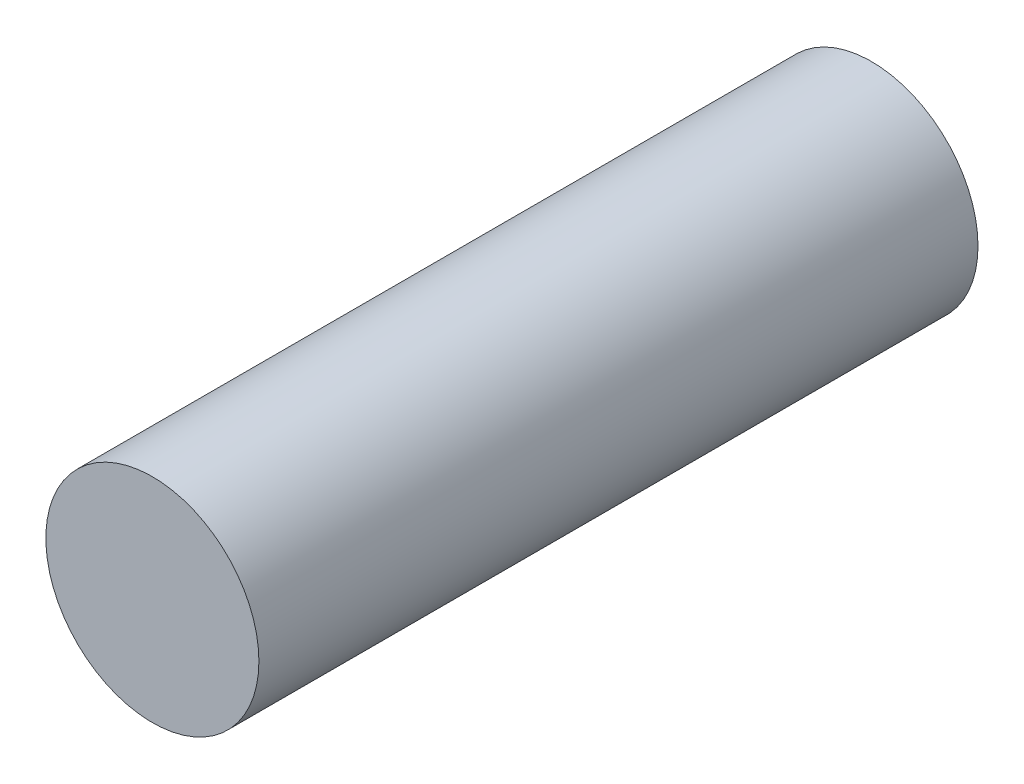
SolidWorks part; units mm, degrees
material "Cast Alloy Steel"
ref_plane "Front Plane" through (0, 0, 0) normal (0, 0, 1) x (1, 0, 0)
ref_plane "Top Plane" through (0, 0, 0) normal (0, 1, 0) x (1, 0, 0)
ref_plane "Right Plane" through (0, 0, 0) normal (1, 0, 0) x (0, 0, -1)
sketch "Sketch1" plane through (0, 0, 0) normal (0, 0, 1) x (1, 0, 0)
  circle A0 centre (0, 0) radius 4
extrude "Boss-Extrude1" add sketch "Sketch1" along normal blind 27
